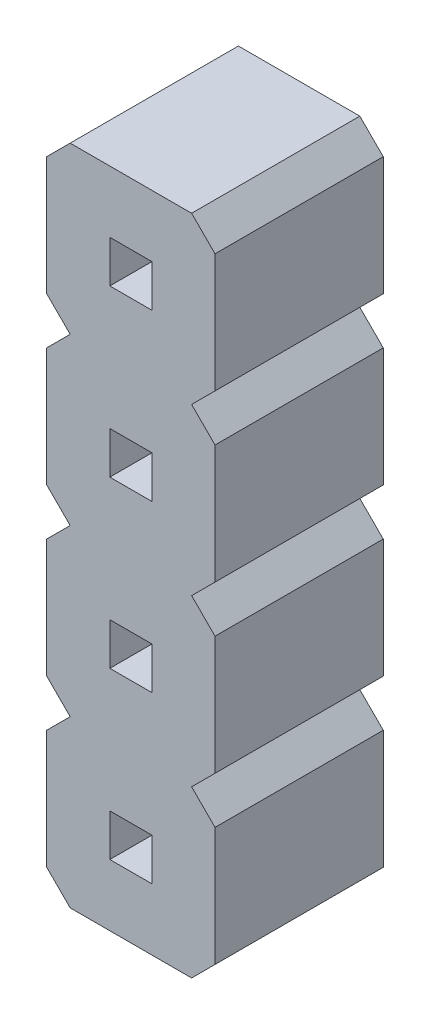
SolidWorks part; units mm, degrees
ref_plane "Alzado" through (0, 0, 0) normal (0, 0, 1) x (1, 0, 0)
ref_plane "Planta" through (0, 0, 0) normal (0, 1, 0) x (1, 0, 0)
ref_plane "Vista lateral" through (0, 0, 0) normal (1, 0, 0) x (0, 0, -1)
sketch "pin_drawing" plane through (0, 0, 0) normal (0, 0, 1) x (1, 0, 0)
  line L0 (0.9525, -0.932) -> (0, -0.932) construction
  line L1 (0, 2.1464) -> (0, 0.3536)
  line L2 (0, -0.3536) -> (0, -2.1464)
  line L3 (0, -0.3536) -> (0.3536, 0)
  line L4 (1.5885, -1.568) -> (2.541, -1.568) construction
  line L5 (0, 2.1464) -> (0.3536, 2.5)
  line L6 (2.541, -0.3536) -> (2.541, -2.1464)
  line L7 (0.9525, -1.25) -> (0.9525, -0.932) construction
  line L8 (2.541, -2.1464) -> (2.1874, -2.5)
  line L9 (2.1874, 0) -> (2.541, -0.3536)
  line L10 (1.5885, -1.25) -> (1.5885, -1.568) construction
  line L11 (0.3536, -2.5) -> (0, -2.1464)
  line L12 (0.9525, -0.932) -> (1.5885, -0.932)
  line L13 (0.9525, -0.932) -> (0.9525, -1.568)
  line L14 (0.9525, -1.568) -> (1.5885, -1.568)
  line L15 (1.5885, -0.932) -> (1.5885, -1.568)
  line L16 (2.541, 2.1464) -> (2.541, 0.3536)
  line L17 (2.541, 0.3536) -> (2.1874, 0)
  line L18 (2.1874, 2.5) -> (2.541, 2.1464)
  line L19 (0.3536, 0) -> (0, 0.3536)
  line L20 (0.9525, 1.568) -> (1.5885, 1.568)
  line L21 (0.9525, 1.568) -> (0.9525, 0.932)
  line L22 (0.9525, 0.932) -> (1.5885, 0.932)
  line L23 (1.5885, 1.568) -> (1.5885, 0.932)
  line L24 (0.9525, 1.568) -> (0, 1.568) construction
  line L25 (1.5885, 0.932) -> (2.541, 0.932) construction
  line L26 (0.9525, 1.25) -> (0.9525, 1.568) construction
  line L27 (1.5885, 1.25) -> (1.5885, 0.932) construction
  line L28 (0, 4.6464) -> (0, 2.8536)
  line L29 (0, 4.6464) -> (0.3536, 5)
  line L30 (2.541, 4.6464) -> (2.541, 2.8536)
  line L31 (2.541, 2.8536) -> (2.1874, 2.5)
  line L32 (2.1874, 5) -> (2.541, 4.6464)
  line L33 (0.3536, 2.5) -> (0, 2.8536)
  line L34 (0.9525, 4.068) -> (1.5885, 4.068)
  line L35 (0.9525, 4.068) -> (0.9525, 3.432)
  line L36 (0.9525, 3.432) -> (1.5885, 3.432)
  line L37 (1.5885, 4.068) -> (1.5885, 3.432)
  line L38 (0.9525, 4.068) -> (0, 4.068) construction
  line L39 (1.5885, 3.432) -> (2.541, 3.432) construction
  line L40 (0.9525, 3.75) -> (0.9525, 4.068) construction
  line L41 (1.5885, 3.75) -> (1.5885, 3.432) construction
  line L42 (0, 7.1464) -> (0, 5.3536)
  line L43 (0, 7.1464) -> (0.3536, 7.5)
  line L44 (2.541, 7.1464) -> (2.541, 5.3536)
  line L45 (2.541, 5.3536) -> (2.1874, 5)
  line L46 (2.1874, 7.5) -> (2.541, 7.1464)
  line L47 (0.3536, 5) -> (0, 5.3536)
  line L48 (0.9525, 6.568) -> (1.5885, 6.568)
  line L49 (0.9525, 6.568) -> (0.9525, 5.932)
  line L50 (0.9525, 5.932) -> (1.5885, 5.932)
  line L51 (1.5885, 6.568) -> (1.5885, 5.932)
  line L52 (0.9525, 6.568) -> (0, 6.568) construction
  line L53 (1.5885, 5.932) -> (2.541, 5.932) construction
  line L54 (0.9525, 6.25) -> (0.9525, 6.568) construction
  line L55 (1.5885, 6.25) -> (1.5885, 5.932) construction
  line L56 (0, 9.6464) -> (0, 7.8536) construction
  line L57 (0, 9.6464) -> (0.3536, 10) construction
  line L58 (2.541, 9.6464) -> (2.541, 7.8536) construction
  line L59 (2.541, 7.8536) -> (2.1874, 7.5) construction
  line L60 (2.1874, 10) -> (2.541, 9.6464) construction
  line L61 (0.3536, 7.5) -> (0, 7.8536) construction
  line L62 (0.9525, 9.068) -> (1.5885, 9.068) construction
  line L63 (0.9525, 9.068) -> (0.9525, 8.432) construction
  line L64 (0.9525, 8.432) -> (1.5885, 8.432) construction
  line L65 (1.5885, 9.068) -> (1.5885, 8.432) construction
  line L66 (0.9525, 9.068) -> (0, 9.068) construction
  line L67 (1.5885, 8.432) -> (2.541, 8.432) construction
  line L68 (0.9525, 8.75) -> (0.9525, 9.068) construction
  line L69 (1.5885, 8.75) -> (1.5885, 8.432) construction
  line L70 (0, 12.1464) -> (0, 10.3536) construction
  line L71 (0, 12.1464) -> (0.3536, 12.5) construction
  line L72 (2.541, 12.1464) -> (2.541, 10.3536) construction
  line L73 (2.541, 10.3536) -> (2.1874, 10) construction
  line L74 (2.1874, 12.5) -> (2.541, 12.1464) construction
  line L75 (0.3536, 10) -> (0, 10.3536) construction
  line L76 (0.9525, 11.568) -> (1.5885, 11.568) construction
  line L77 (0.9525, 11.568) -> (0.9525, 10.932) construction
  line L78 (0.9525, 10.932) -> (1.5885, 10.932) construction
  line L79 (1.5885, 11.568) -> (1.5885, 10.932) construction
  line L80 (0.9525, 11.568) -> (0, 11.568) construction
  line L81 (1.5885, 10.932) -> (2.541, 10.932) construction
  line L82 (0.9525, 11.25) -> (0.9525, 11.568) construction
  line L83 (1.5885, 11.25) -> (1.5885, 10.932) construction
  line L84 (0, 14.6464) -> (0, 12.8536) construction
  line L85 (0, 14.6464) -> (0.3536, 15) construction
  line L86 (2.541, 14.6464) -> (2.541, 12.8536) construction
  line L87 (2.541, 12.8536) -> (2.1874, 12.5) construction
  line L88 (2.1874, 15) -> (2.541, 14.6464) construction
  line L89 (0.3536, 12.5) -> (0, 12.8536) construction
  line L90 (0.9525, 14.068) -> (1.5885, 14.068) construction
  line L91 (0.9525, 14.068) -> (0.9525, 13.432) construction
  line L92 (0.9525, 13.432) -> (1.5885, 13.432) construction
  line L93 (1.5885, 14.068) -> (1.5885, 13.432) construction
  line L94 (0.9525, 14.068) -> (0, 14.068) construction
  line L95 (1.5885, 13.432) -> (2.541, 13.432) construction
  line L96 (0.9525, 13.75) -> (0.9525, 14.068) construction
  line L97 (1.5885, 13.75) -> (1.5885, 13.432) construction
  line L98 (0, 17.1464) -> (0, 15.3536) construction
  line L99 (0, 17.1464) -> (0.3536, 17.5) construction
  line L100 (2.541, 17.1464) -> (2.541, 15.3536) construction
  line L101 (2.541, 15.3536) -> (2.1874, 15) construction
  line L102 (2.1874, 17.5) -> (2.541, 17.1464) construction
  line L103 (0.3536, 15) -> (0, 15.3536) construction
  line L104 (0.9525, 16.568) -> (1.5885, 16.568) construction
  line L105 (0.9525, 16.568) -> (0.9525, 15.932) construction
  line L106 (0.9525, 15.932) -> (1.5885, 15.932) construction
  line L107 (1.5885, 16.568) -> (1.5885, 15.932) construction
  line L108 (0.9525, 16.568) -> (0, 16.568) construction
  line L109 (1.5885, 15.932) -> (2.541, 15.932) construction
  line L110 (0.9525, 16.25) -> (0.9525, 16.568) construction
  line L111 (1.5885, 16.25) -> (1.5885, 15.932) construction
  line L112 (0, 19.6464) -> (0, 17.8536) construction
  line L113 (0, 19.6464) -> (0.3536, 20) construction
  line L114 (2.541, 19.6464) -> (2.541, 17.8536) construction
  line L115 (2.541, 17.8536) -> (2.1874, 17.5) construction
  line L116 (2.1874, 20) -> (2.541, 19.6464) construction
  line L117 (0.3536, 17.5) -> (0, 17.8536) construction
  line L118 (0.9525, 19.068) -> (1.5885, 19.068) construction
  line L119 (0.9525, 19.068) -> (0.9525, 18.432) construction
  line L120 (0.9525, 18.432) -> (1.5885, 18.432) construction
  line L121 (1.5885, 19.068) -> (1.5885, 18.432) construction
  line L122 (0.9525, 19.068) -> (0, 19.068) construction
  line L123 (1.5885, 18.432) -> (2.541, 18.432) construction
  line L124 (0.9525, 18.75) -> (0.9525, 19.068) construction
  line L125 (1.5885, 18.75) -> (1.5885, 18.432) construction
  line L126 (0, 22.1464) -> (0, 20.3536) construction
  line L127 (0, 22.1464) -> (0.3536, 22.5) construction
  line L128 (2.541, 22.1464) -> (2.541, 20.3536) construction
  line L129 (2.541, 20.3536) -> (2.1874, 20) construction
  line L130 (2.1874, 22.5) -> (2.541, 22.1464) construction
  line L131 (0.3536, 20) -> (0, 20.3536) construction
  line L132 (0.9525, 21.568) -> (1.5885, 21.568) construction
  line L133 (0.9525, 21.568) -> (0.9525, 20.932) construction
  line L134 (0.9525, 20.932) -> (1.5885, 20.932) construction
  line L135 (1.5885, 21.568) -> (1.5885, 20.932) construction
  line L136 (0.9525, 21.568) -> (0, 21.568) construction
  line L137 (1.5885, 20.932) -> (2.541, 20.932) construction
  line L138 (0.9525, 21.25) -> (0.9525, 21.568) construction
  line L139 (1.5885, 21.25) -> (1.5885, 20.932) construction
  line L140 (0, 24.6464) -> (0, 22.8536) construction
  line L141 (0, 24.6464) -> (0.3536, 25) construction
  line L142 (2.541, 24.6464) -> (2.541, 22.8536) construction
  line L143 (2.541, 22.8536) -> (2.1874, 22.5) construction
  line L144 (2.1874, 25) -> (2.541, 24.6464) construction
  line L145 (0.3536, 22.5) -> (0, 22.8536) construction
  line L146 (0.9525, 24.068) -> (1.5885, 24.068) construction
  line L147 (0.9525, 24.068) -> (0.9525, 23.432) construction
  line L148 (0.9525, 23.432) -> (1.5885, 23.432) construction
  line L149 (1.5885, 24.068) -> (1.5885, 23.432) construction
  line L150 (0.9525, 24.068) -> (0, 24.068) construction
  line L151 (1.5885, 23.432) -> (2.541, 23.432) construction
  line L152 (0.9525, 23.75) -> (0.9525, 24.068) construction
  line L153 (1.5885, 23.75) -> (1.5885, 23.432) construction
  line L154 (0, 27.1464) -> (0, 25.3536) construction
  line L155 (0, 27.1464) -> (0.3536, 27.5) construction
  line L156 (2.541, 27.1464) -> (2.541, 25.3536) construction
  line L157 (2.541, 25.3536) -> (2.1874, 25) construction
  line L158 (2.1874, 27.5) -> (2.541, 27.1464) construction
  line L159 (0.3536, 25) -> (0, 25.3536) construction
  line L160 (0.9525, 26.568) -> (1.5885, 26.568) construction
  line L161 (0.9525, 26.568) -> (0.9525, 25.932) construction
  line L162 (0.9525, 25.932) -> (1.5885, 25.932) construction
  line L163 (1.5885, 26.568) -> (1.5885, 25.932) construction
  line L164 (0.9525, 26.568) -> (0, 26.568) construction
  line L165 (1.5885, 25.932) -> (2.541, 25.932) construction
  line L166 (0.9525, 26.25) -> (0.9525, 26.568) construction
  line L167 (1.5885, 26.25) -> (1.5885, 25.932) construction
  line L168 (2.1874, -2.5) -> (0.3536, -2.5)
  line L169 (0.3536, 27.5) -> (2.1874, 27.5) construction
  line L170 (2.1874, 7.5) -> (0.3536, 7.5)
  dimension "D1" = 0.318
  dimension "D2" = 0.9525
  dimension "D3" = 0.5
  dimension "D4" = 135
  dimension "D5" = 0.5
  dimension "D6" = 135
  dimension "D7" = 12
extrude "Boss-Extrude1" add sketch "pin_drawing" along normal blind 2.54
